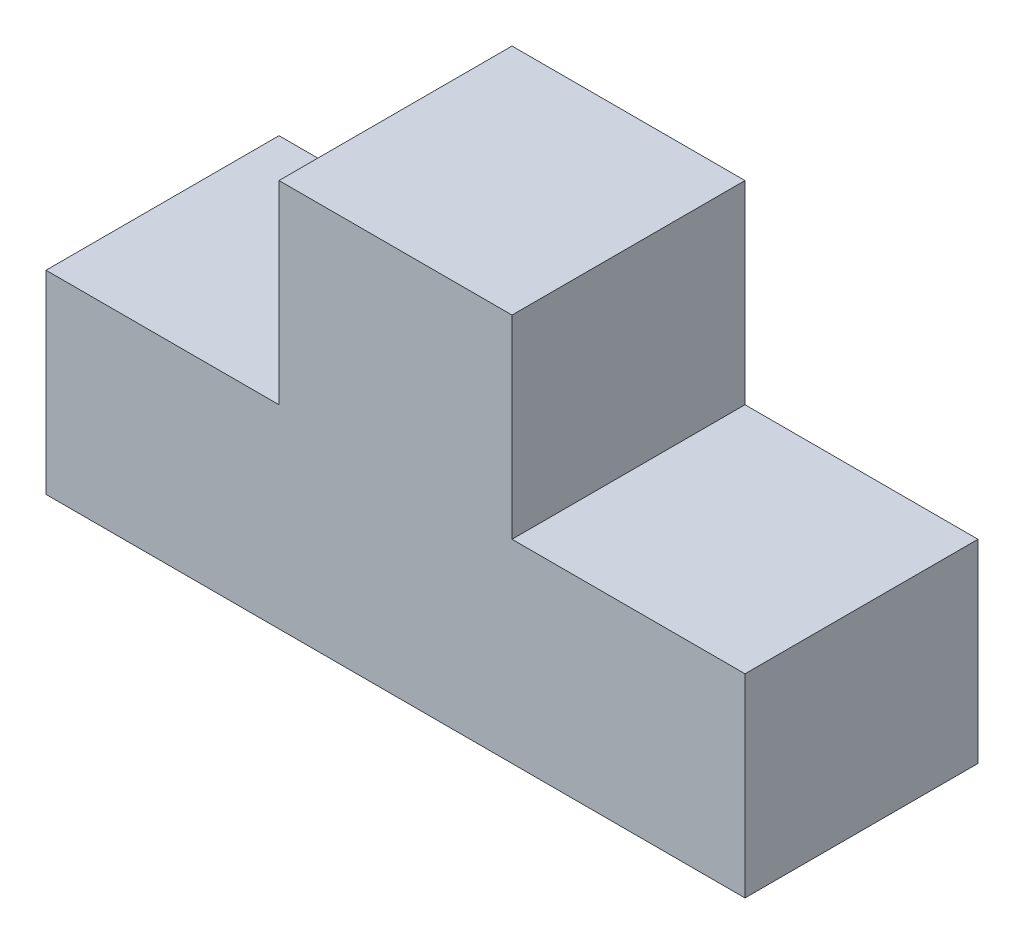
SolidWorks part; units mm, degrees
ref_plane "Front Plane" through (0, 0, 0) normal (0, 0, 1) x (1, 0, 0)
ref_plane "Top Plane" through (0, 0, 0) normal (0, 1, 0) x (1, 0, 0)
ref_plane "Right Plane" through (0, 0, 0) normal (1, 0, 0) x (0, 0, -1)
sketch "Sketch1" plane through (0, 0, 0) normal (0, 0, 1) x (1, 0, 0)
  line L0 (0, 28.3366) -> (0, -37.6656) construction
  line L1 (-45, 0) -> (45, 0)
  line L2 (45, 0) -> (45, 25)
  line L3 (45, 25) -> (15, 25)
  line L4 (15, 25) -> (15, 50)
  line L5 (15, 50) -> (-15, 50)
  line L6 (0, 28.3366) -> (0, 69.6171) construction
  line L7 (-15, 25) -> (-15, 50)
  line L8 (-45, 25) -> (-15, 25)
  line L9 (-45, 0) -> (-45, 25)
  point P5 (0, 0)
  point P14 (0, 50)
  dimension "D1" = 90
  dimension "D2" = 25
  dimension "D3" = 30
  dimension "D4" = 50
extrude "Boss-Extrude1" add sketch "Sketch1" along normal blind 30
